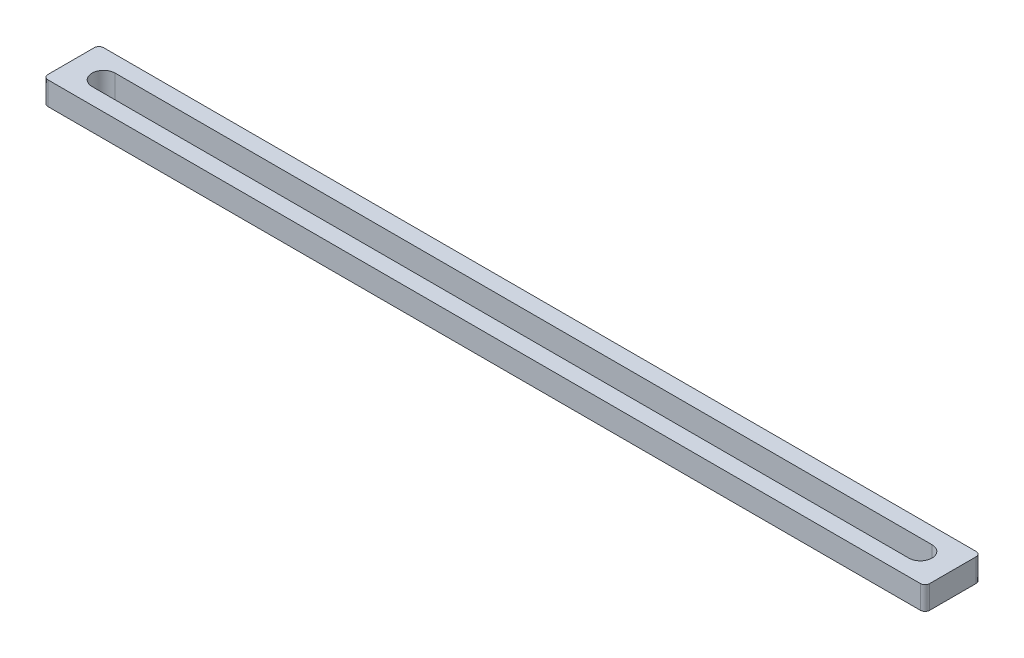
SolidWorks part; units mm, degrees
ref_plane "Plan de face" through (0, 0, 0) normal (0, 0, 1) x (1, 0, 0)
ref_plane "Plan de dessus" through (0, 0, 0) normal (0, 1, 0) x (1, 0, 0)
ref_plane "Plan de droite" through (0, 0, 0) normal (1, 0, 0) x (0, 0, -1)
sketch "Esquisse1" plane through (0, 0, 0) normal (0, 1, 0) x (1, 0, 0)
  line L0 (-88, 0) -> (88, 0) construction
  line L1 (-95, -6) -> (95, -6)
  line L2 (-95, -6) -> (-95, 6)
  line L3 (-95, 6) -> (95, 6)
  line L4 (95, -6) -> (95, 6)
  line L5 (-95, -6) -> (95, 6) construction
  line L6 (-95, 6) -> (95, -6) construction
  line L7 (-88, 2.5) -> (88, 2.5)
  line L8 (-88, -2.5) -> (88, -2.5)
  arc A0 (-88, 2.5) -> (-88, -2.5) centre (-88, 0) ccw
  arc A1 (88, -2.5) -> (88, 2.5) centre (88, 0) ccw
  point P0 (0, 0)
  point P8 (0, 0)
  dimension "D2" = 2.5
  dimension "D1" = 7
  dimension "D3" = 12
  dimension "D4" = 7
  dimension "D5" = 190
extrude "Boss.-Extru.1" add sketch "Esquisse1" along normal mid plane 5
fillet "Congé2" radius 1 4 edges at (95, 0, -6) (-95, 0, -6) (-95, 0, 6) (95, 0, 6)
